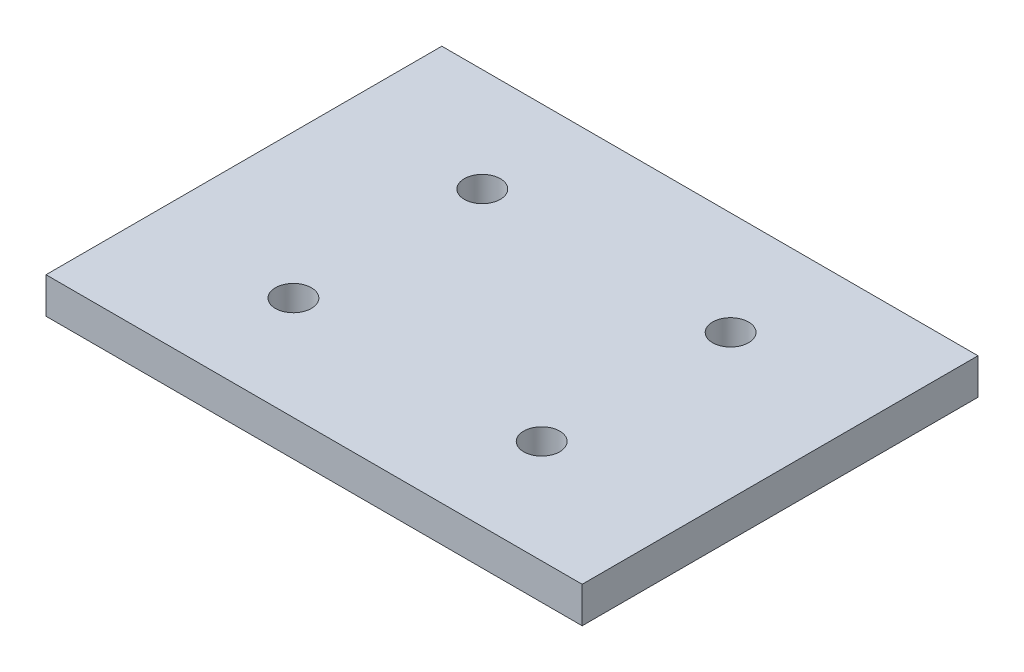
SolidWorks part; units mm, degrees
ref_plane "Front Plane" through (0, 0, 0) normal (0, 0, 1) x (1, 0, 0)
ref_plane "Top Plane" through (0, 0, 0) normal (0, 1, 0) x (1, 0, 0)
ref_plane "Right Plane" through (0, 0, 0) normal (1, 0, 0) x (0, 0, -1)
sketch "Sketch1" plane through (0, 0, 0) normal (0, 1, 0) x (1, 0, 0)
  line L1 (-14.9, -11) -> (14.9, -11)
  line L2 (-14.9, -11) -> (-14.9, 11)
  line L3 (-14.9, 11) -> (14.9, 11)
  line L4 (14.9, -11) -> (14.9, 11)
  line L5 (-14.9, -11) -> (14.9, 11) construction
  line L6 (-14.9, 11) -> (14.9, -11) construction
  circle A0 centre (10.15, 8) radius 1 construction
  circle A1 centre (10.15, -8) radius 1 construction
  circle A2 centre (-10.15, -8) radius 1 construction
  circle A3 centre (-10.15, 8) radius 1 construction
  point P0 (0, 0)
  dimension "D11" = 2
  dimension "D12" = 2
  dimension "D13" = 2
  dimension "D14" = 2
  dimension "D1" = 29.8
  dimension "D2" = 22
  dimension "D3" = 4.75
  dimension "D4" = 3
  dimension "D5" = 3
  dimension "D6" = 4.75
  dimension "D7" = 4.75
  dimension "D8" = 4.75
  dimension "D9" = 3
  dimension "D10" = 3
extrude "Boss-Extrude1" add sketch "Sketch1" along normal blind 2
sketch "Sketch2" plane through (0, 0, 0) normal (0, -1, 0) x (1, 0, 0)
  line L0 (14.9, -11) -> (-14.9, -11) construction
  line L1 (14.9, 11) -> (14.9, -11) construction
  line L2 (-14.9, -11) -> (-14.9, 11) construction
  circle A0 centre (6.9, -5.25) radius 1
  circle A1 centre (-6.9, -5.25) radius 1
  dimension "D5" = 2
  dimension "D6" = 2
  dimension "D1" = 5.75
  dimension "D2" = 5.75
  dimension "D3" = 8
  dimension "D4" = 8
ref_plane "Plane1" through (0, 0, 0) normal (0, 0, -1) x (-1, 0, 0)
extrude "Cut-Extrude2" cut sketch "Sketch2" against normal blind 10
mirror "Mirror1" about plane through (0, 0, 0) normal (0, 0, -1) of "Cut-Extrude2"
